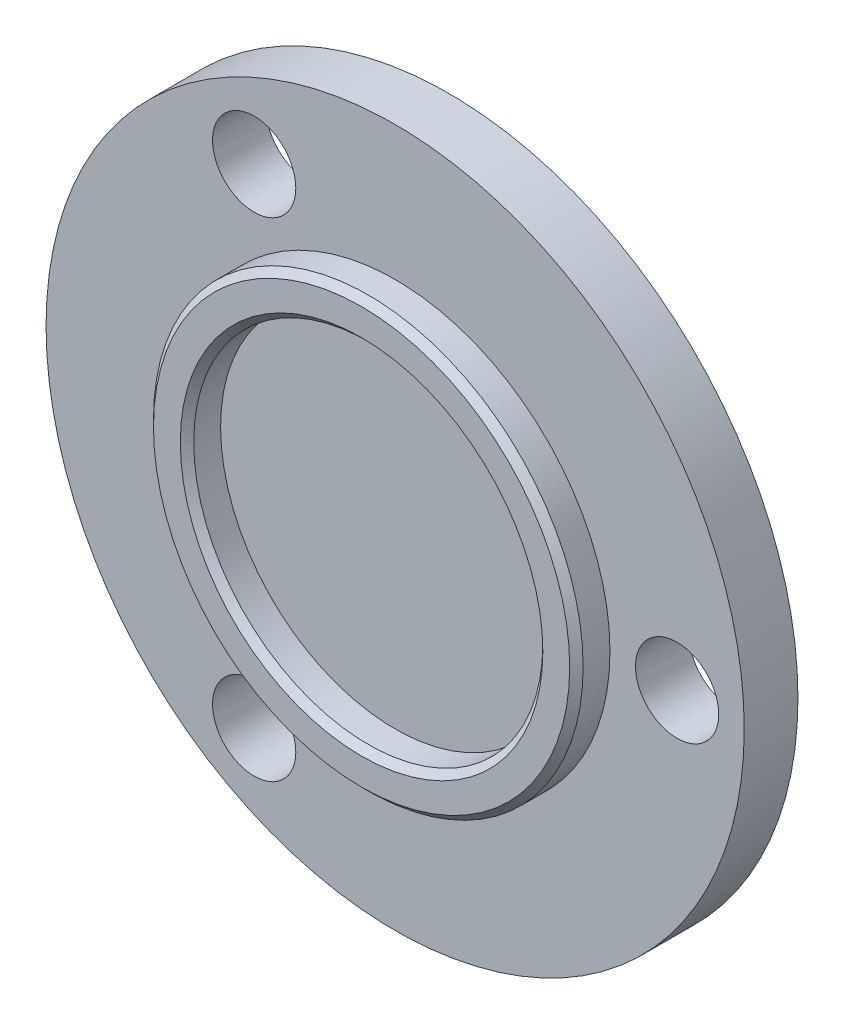
SolidWorks part; units mm, degrees
ref_plane "Front Plane" through (0, 0, 0) normal (0, 0, 1) x (1, 0, 0)
ref_plane "Top Plane" through (0, 0, 0) normal (0, 1, 0) x (1, 0, 0)
ref_plane "Right Plane" through (0, 0, 0) normal (1, 0, 0) x (0, 0, -1)
sketch "Sketch1" plane through (0, 0, 0) normal (0, 0, 1) x (1, 0, 0)
  circle A0 centre (0, 0) radius 26
  dimension "D1" = 52
extrude "Boss-Extrude1" add sketch "Sketch1" along normal blind 4
sketch "Sketch2" plane through (0, 0, 4) normal (0, 0, 1) x (1, 0, 0)
  line L0 (0, 0) -> (21, 0) construction
  line L1 (0, 0) -> (-10.5, -18.1865) construction
  circle A0 centre (0, 0) radius 21
  circle A1 centre (21, 0) radius 3.1
  circle A2 centre (-10.5, -18.1865) radius 3.1
  circle A3 centre (-10.5, 18.1865) radius 3.1
  dimension "D1" = 42
  dimension "D2" = 6.2
  dimension "D4" = 120
  dimension "D3" = 3
extrude "Cut-Extrude1" cut sketch "Sketch2" against normal blind 4 contours A2 | A1 | A3
sketch "Sketch4" plane through (0, 0, 4) normal (0, 0, 1) x (1, 0, 0)
  circle A0 centre (0, 0) radius 16
  circle A1 centre (0, 0) radius 13
  dimension "D1" = 32
  dimension "D2" = 26
extrude "Boss-Extrude2" add sketch "Sketch4" along normal blind 2.5
chamfer "Chamfer1" distance 0.5 angle 45 1 edges at (16, 0, 6.5)
chamfer "Chamfer2" distance 0.5 angle 45 1 edges at (13, 0, 6.5)
